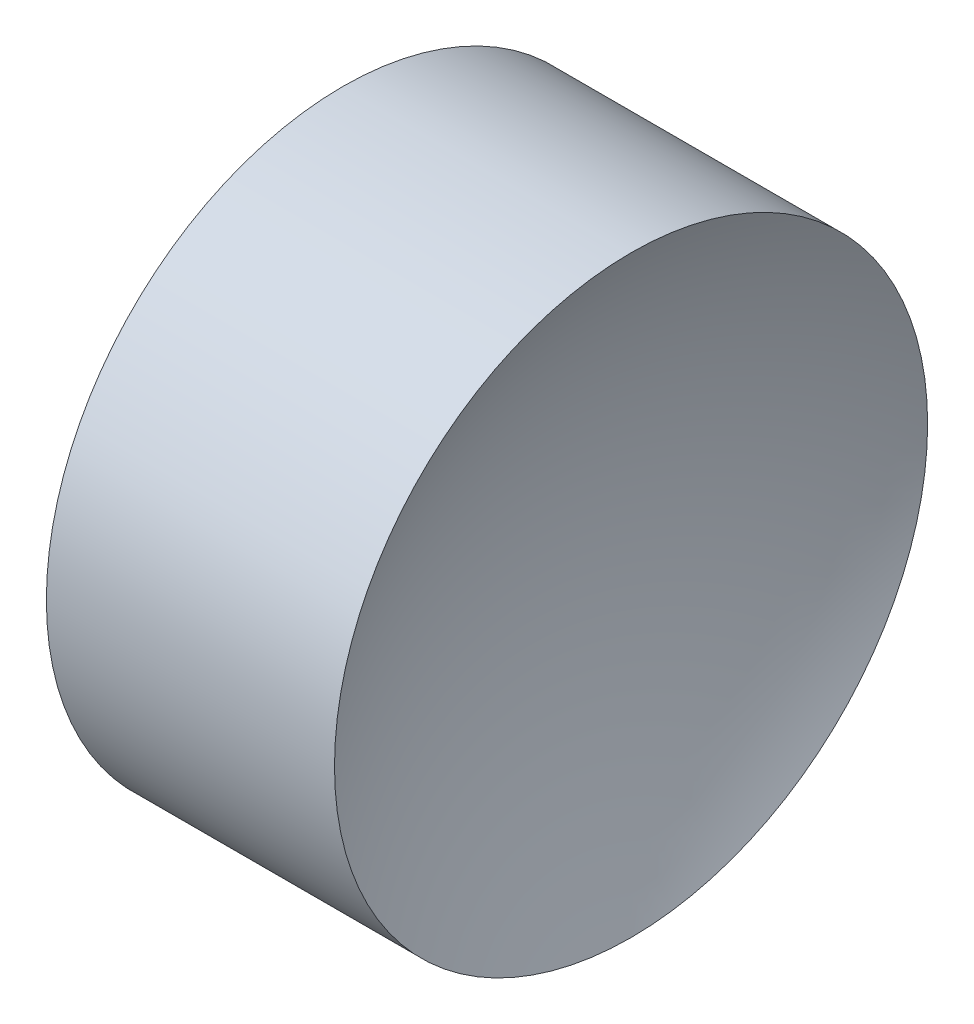
SolidWorks part; units mm, degrees
ref_plane "前视基准面" through (0, 0, 0) normal (0, 0, 1) x (1, 0, 0)
ref_plane "上视基准面" through (0, 0, 0) normal (0, 1, 0) x (1, 0, 0)
ref_plane "右视基准面" through (0, 0, 0) normal (1, 0, 0) x (0, 0, -1)
sketch "草图2" plane through (0, 0, 0) normal (0, 0, 1) x (1, 0, 0)
  line L0 (21.2249, 13.0445) -> (27.8323, 13.0445) construction
  line L1 (23.2619, 13.0445) -> (24.7619, 13.0445)
  line L3 (24.0119, 16.1945) -> (25.5419, 16.1945)
  line L4 (24.0119, 16.1945) -> (22.4818, 16.1945)
  arc A0 (25.5419, 16.1945) -> (24.7619, 13.0445) centre (31.5119, 13.0445) ccw
  arc A1 (23.2619, 13.0445) -> (22.4818, 16.1945) centre (16.5119, 13.0445) ccw
revolve "旋转1" add sketch "草图2" angle 360 about L0
